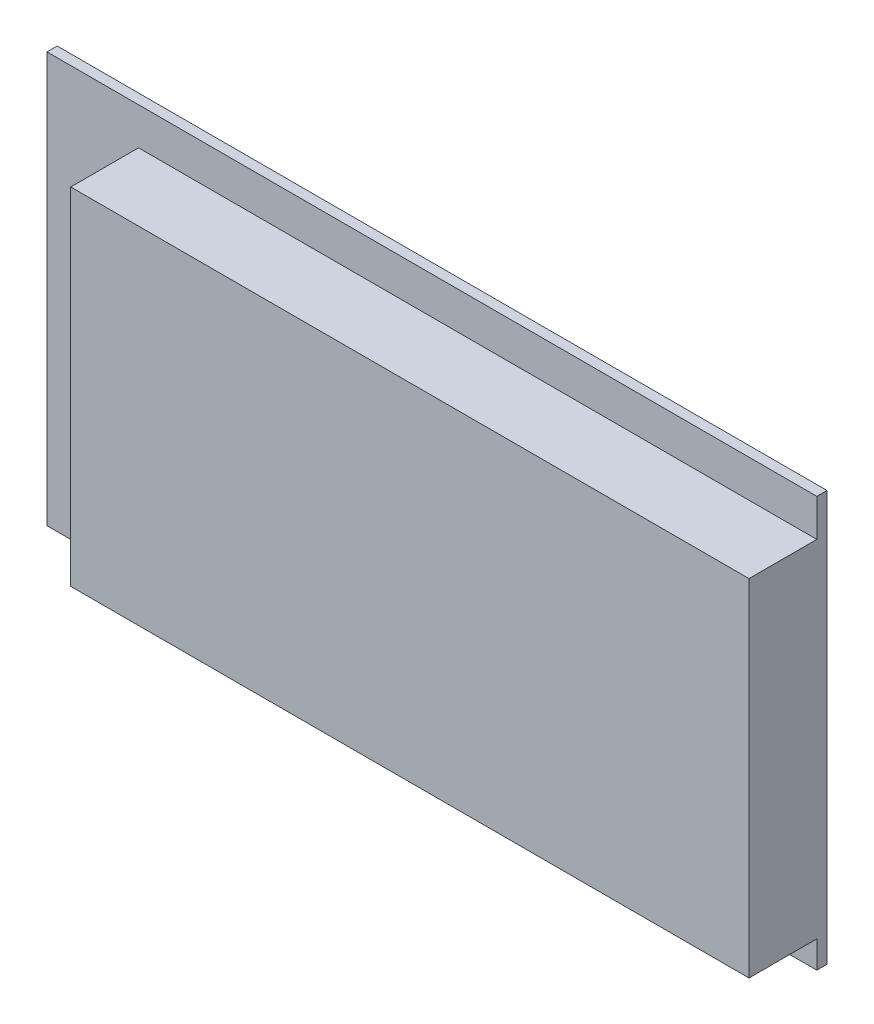
SolidWorks part; units mm, degrees
ref_plane "Plan de face" through (0, 0, 0) normal (0, 0, 1) x (1, 0, 0)
ref_plane "Plan de dessus" through (0, 0, 0) normal (0, 1, 0) x (1, 0, 0)
ref_plane "Plan de droite" through (0, 0, 0) normal (1, 0, 0) x (0, 0, -1)
sketch "Esquisse1" plane through (0, 0, 0) normal (0, 0, 1) x (1, 0, 0)
  line L1 (0, 0) -> (113.5, 0)
  line L2 (0, 0) -> (0, 60.5)
  line L3 (0, 60.5) -> (113.5, 60.5)
  line L4 (113.5, 0) -> (113.5, 60.5)
  dimension "D1" = 60.5
  dimension "D2" = 113.5
extrude "Boss.-Extru.1" add sketch "Esquisse1" along normal blind 1.5
sketch "Esquisse2" plane through (0, 0, 1.5) normal (0, 0, 1) x (1, 0, 0)
  line L0 (113.5, 60.5) -> (0, 60.5) construction
  line L1 (13.5, 4) -> (113.5, 4)
  line L2 (13.5, 4) -> (13.5, 55)
  line L3 (13.5, 55) -> (113.5, 55)
  line L4 (113.5, 4) -> (113.5, 55)
  line L5 (0, 0) -> (113.5, 0) construction
  line L6 (113.5, 0) -> (113.5, 60.5) construction
  dimension "D1" = 5.5
  dimension "D2" = 4
  dimension "D3" = 100
  dimension "D4" = 0
extrude "Boss.-Extru.2" add sketch "Esquisse2" along normal blind 10
